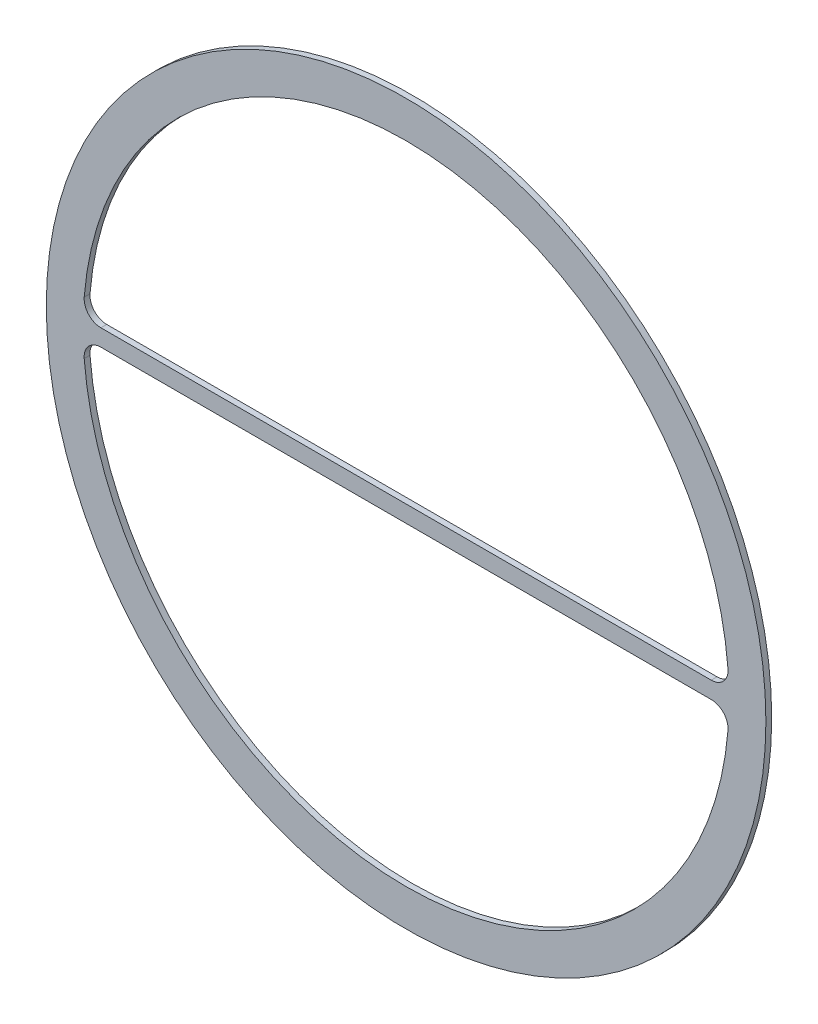
SolidWorks part; units mm, degrees
ref_plane "Front Plane" through (0, 0, 0) normal (0, 0, 1) x (1, 0, 0)
ref_plane "Top Plane" through (0, 0, 0) normal (0, 1, 0) x (1, 0, 0)
ref_plane "Right Plane" through (0, 0, 0) normal (1, 0, 0) x (0, 0, -1)
sketch "Sketch1" plane through (0, 0, 0) normal (0, 0, 1) x (1, 0, 0)
  line L1 (249.9155, -6.5) -> (-249.9155, -6.5)
  line L3 (249.9155, 6.5) -> (-249.9155, 6.5)
  arc A0 (249.9155, 6.5) -> (-249.9155, 6.5) centre (0, 0) ccw
  circle A1 centre (0, 0) radius 278.5
  arc A2 (-249.9155, -6.5) -> (249.9155, -6.5) centre (0, 0) ccw
  dimension "D1" = 500
  dimension "D2" = 557
  dimension "D3" = 13
extrude "Boss-Extrude1" add sketch "Sketch1" along normal mid plane 4.5
fillet "Fillet1" radius 13 4 edges at (-249.9155, -6.5, 0) (249.9155, -6.5, 0) (-249.9155, 6.5, 0) (249.9155, 6.5, 0)
